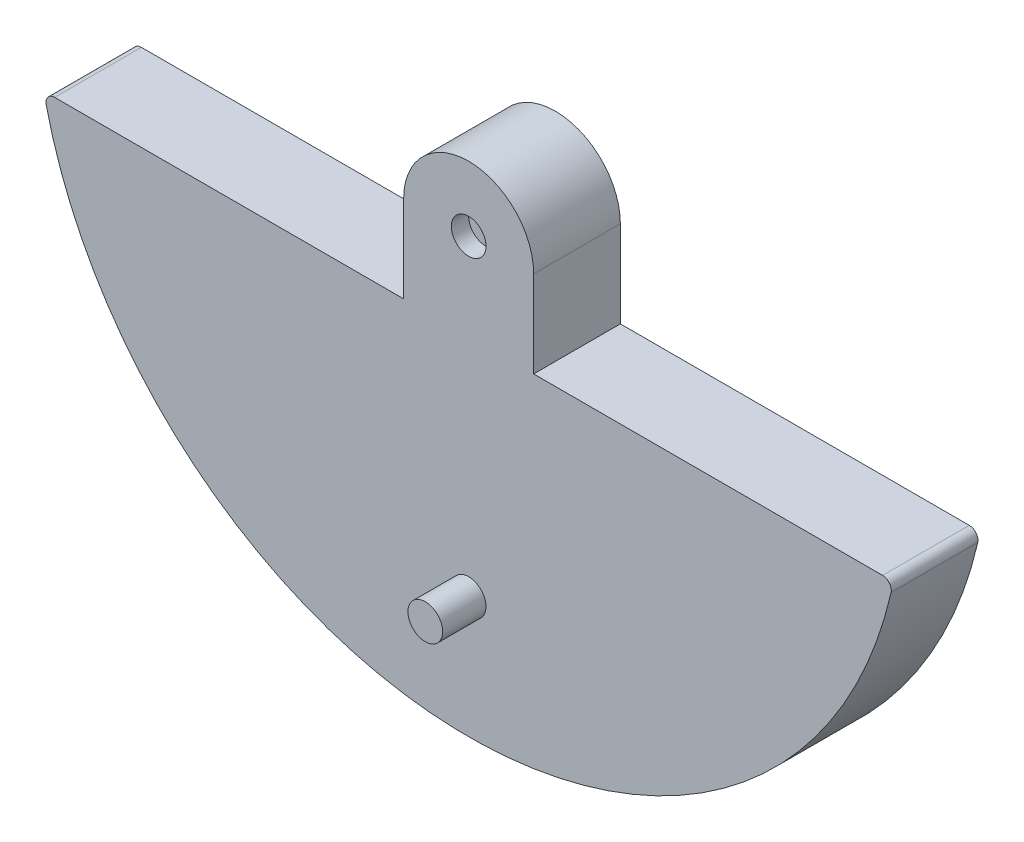
SolidWorks part; units mm, degrees
ref_plane "Front Plane" through (0, 0, 0) normal (0, 0, 1) x (1, 0, 0)
ref_plane "Top Plane" through (0, 0, 0) normal (0, 1, 0) x (1, 0, 0)
ref_plane "Right Plane" through (0, 0, 0) normal (1, 0, 0) x (0, 0, -1)
sketch "Sketch1" plane through (0, 0, 0) normal (0, 0, 1) x (1, 0, 0)
  line L0 (-37.5, 0) -> (-37.5, -100)
  line L1 (-37.5, -100) -> (37.5, -100)
  line L2 (37.5, -100) -> (37.5, 0)
  arc A0 (37.5, 0) -> (-37.5, 0) centre (0, 0) ccw
  dimension "D1" = 75
  dimension "D2" = 100
extrude "Boss-Extrude1" add sketch "Sketch1" along normal blind 50
sketch "Sketch2" plane through (0, 0, 50) normal (0, 0, 1) x (1, 0, 0)
  circle A0 centre (0, 0) radius 10
  dimension "D1" = 20
extrude "Cut-Extrude1" cut sketch "Sketch2" against normal blind 10
sketch "Sketch3" plane through (0, 0, 50) normal (0, 0, 1) x (1, 0, 0)
  line L0 (0, 0) -> (0, -50) construction
  line L2 (-244.949, -50) -> (244.949, -50)
  arc A1 (-244.949, -50) -> (244.949, -50) centre (0, 0) ccw
  dimension "D3" = 250
  dimension "D2" = 50
extrude "Boss-Extrude2" add sketch "Sketch3" against normal blind 50
fillet "Fillet1" radius 5 2 edges at (-244.949, -50, 25) (244.949, -50, 25)
sketch "Sketch4" plane through (0, 0, 50) normal (0, 0, 1) x (1, 0, 0)
  circle A0 centre (0, -180) radius 10
  dimension "D1" = 20
  dimension "D2" = 180
extrude "Boss-Extrude3" add sketch "Sketch4" along normal blind 25 separate body
